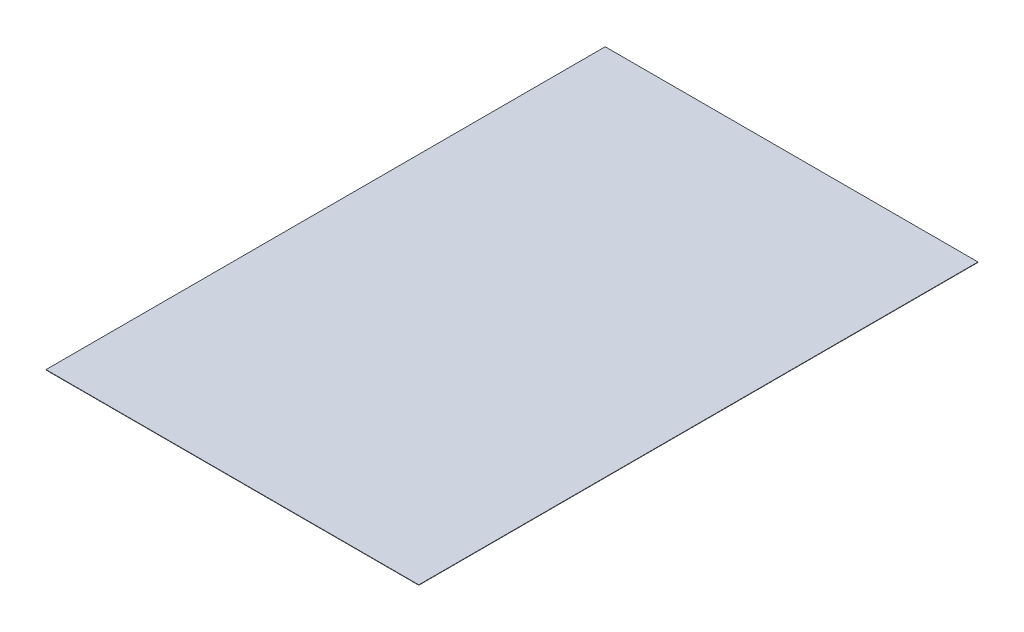
SolidWorks part; units mm, degrees
material "PE High Density"
ref_plane "Front Plane" through (0, 0, 0) normal (0, 0, 1) x (1, 0, 0)
ref_plane "Top Plane" through (0, 0, 0) normal (0, 1, 0) x (1, 0, 0)
ref_plane "Right Plane" through (0, 0, 0) normal (1, 0, 0) x (0, 0, -1)
sketch "Sketch1" plane through (0, 0, 0) normal (0, 1, 0) x (1, 0, 0)
  line L1 (-3048, -4572) -> (3048, -4572)
  line L2 (-3048, -4572) -> (-3048, 4572)
  line L3 (-3048, 4572) -> (3048, 4572)
  line L4 (3048, -4572) -> (3048, 4572)
  line L5 (-3048, -4572) -> (3048, 4572) construction
  line L6 (-3048, 4572) -> (3048, -4572) construction
  point P0 (0, 0)
  dimension "D1" = 6096
  dimension "D2" = 9144
extrude "Boss-Extrude1" add sketch "Sketch1" along normal blind 6
